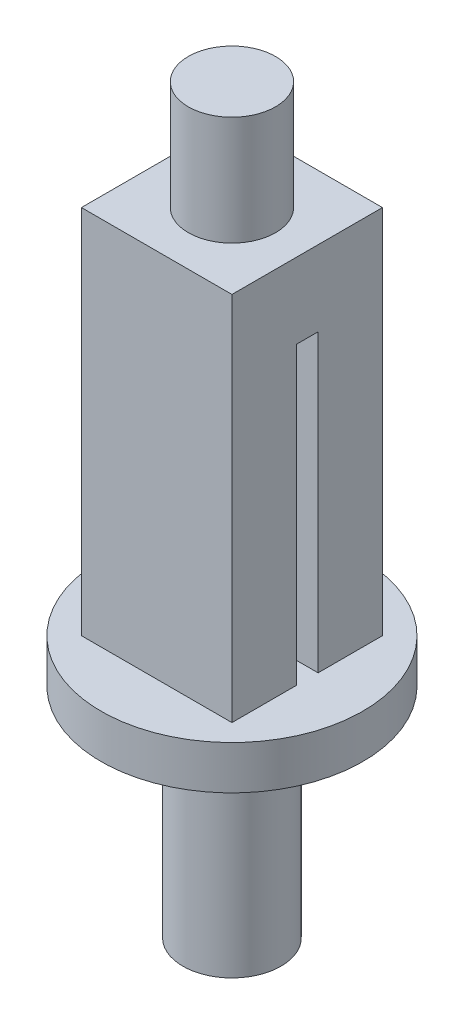
SolidWorks part; units mm, degrees
ref_plane "前视基准面" through (0, 0, 0) normal (0, 0, 1) x (1, 0, 0)
ref_plane "上视基准面" through (0, 0, 0) normal (0, 1, 0) x (1, 0, 0)
ref_plane "右视基准面" through (0, 0, 0) normal (1, 0, 0) x (0, 0, -1)
sketch "草图2" plane through (0, 0, 0) normal (0, 1, 0) x (1, 0, 0)
  line L1 (-3.5684, 4.0757) -> (3.3316, 4.0757)
  line L2 (-3.5684, 4.0757) -> (-3.5684, -2.8243)
  line L3 (-3.5684, -2.8243) -> (3.3316, -2.8243)
  line L4 (3.3316, 4.0757) -> (3.3316, -2.8243)
  dimension "D1" = 6.9
  dimension "D2" = 6.9
extrude "凸台-拉伸1" add sketch "草图2" along normal blind 17
sketch "草图3" plane through (0, 17, 0) normal (0, 1, 0) x (1, 0, 0)
  circle A0 centre (-0.1184, 0.6257) radius 2
  dimension "D1" = 4
extrude "凸台-拉伸2" add sketch "草图3" along normal blind 5
sketch "草图4" plane through (-3.5684, 0, 0) normal (-1, 0, 0) x (0, 0, 1)
  line L0 (-0.6257, -2.5095) -> (-0.6257, 23.1738) construction
  line L1 (2.8243, 17) -> (2.8243, 0) construction
  line L3 (-4.0757, 0) -> (2.8243, 0) construction
  line L4 (-1.1257, 0) -> (-0.1257, 0)
  line L5 (-1.1257, 0) -> (-1.1257, 13.5425)
  line L6 (-1.1257, 13.5425) -> (-0.1257, 13.5425)
  line L7 (-0.1257, 0) -> (-0.1257, 13.5425)
  dimension "D1" = 3.45
  dimension "D2" = 1
  dimension "D3" = 0.5
extrude "切除-拉伸1" cut sketch "草图4" against normal blind 15
sketch "草图5" plane through (0, 0, 0) normal (0, -1, 0) x (1, 0, 0)
  circle A0 centre (-0.1184, -0.6257) radius 6
  dimension "D1" = 12
extrude "凸台-拉伸3" add sketch "草图5" along normal blind 2
sketch "草图6" plane through (0, -2, 0) normal (0, -1, 0) x (1, 0, 0)
  circle A0 centre (-0.1184, -0.6257) radius 2.25
  dimension "D1" = 4.5
extrude "凸台-拉伸4" add sketch "草图6" along normal blind 10
sketch "草图7" plane through (0, -12, 0) normal (0, -1, 0) x (1, 0, 0)
  circle A0 centre (-0.1184, -0.6257) radius 1.5
  dimension "D1" = 3
extrude "切除-拉伸2" cut sketch "草图7" against normal up to surface (25.5425 mm away) up to face at (-0.1184, 13.5425, -0.6257)
